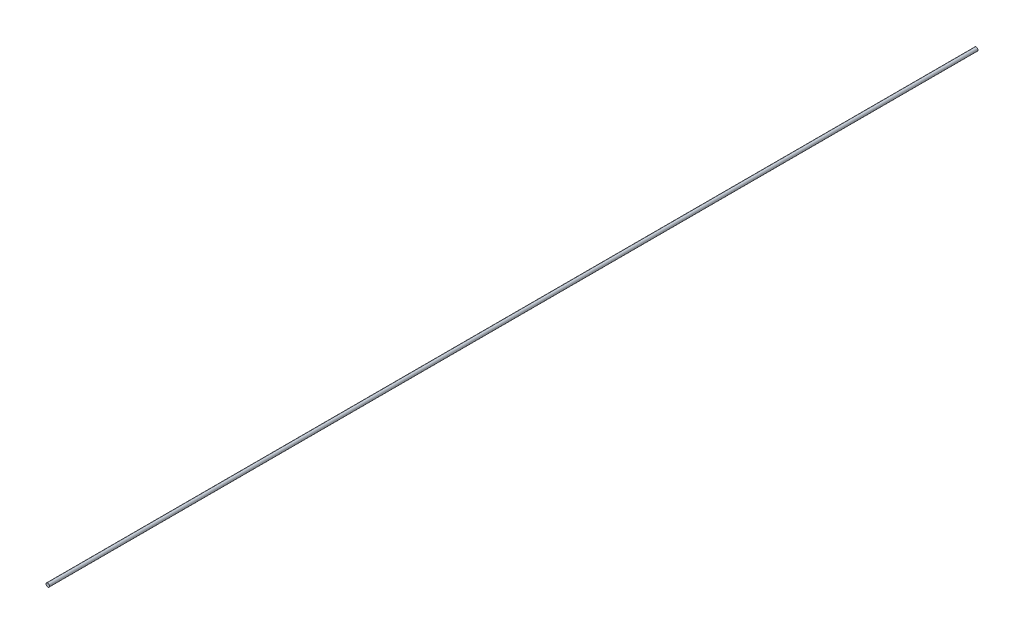
SolidWorks part; units mm, degrees
ref_plane "Front Plane" through (0, 0, 0) normal (0, 0, 1) x (1, 0, 0)
ref_plane "Top Plane" through (0, 0, 0) normal (0, 1, 0) x (1, 0, 0)
ref_plane "Right Plane" through (0, 0, 0) normal (1, 0, 0) x (0, 0, -1)
sketch "Sketch1" plane through (0, 0, 0) normal (0, 0, 1) x (1, 0, 0)
  circle A0 centre (0, 0) radius 3.8
  dimension "D1" = 7.6
extrude "Boss-Extrude1" add sketch "Sketch1" along normal blind 2000
